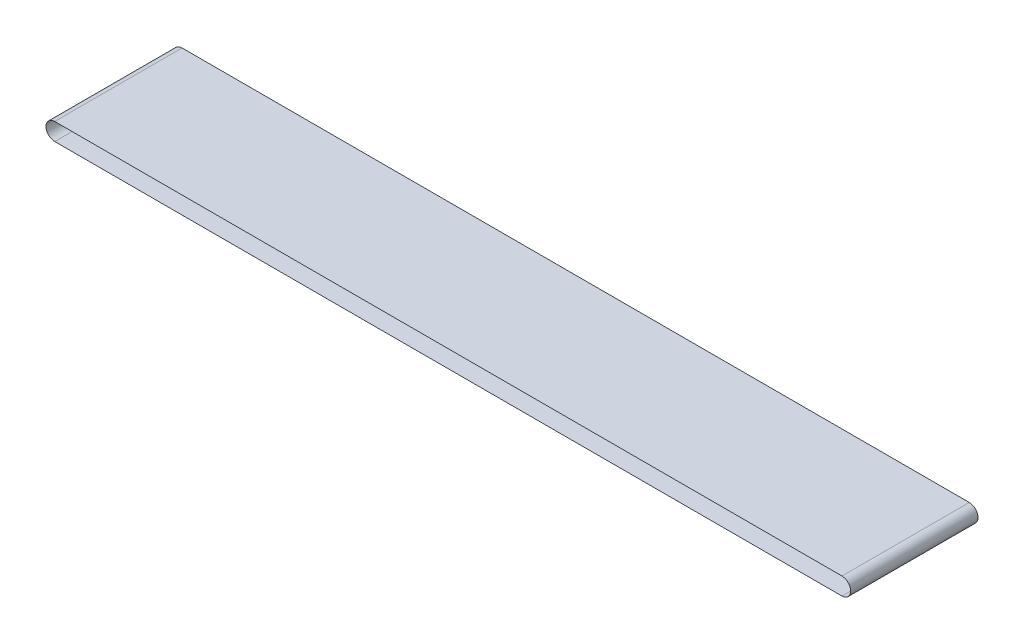
SolidWorks part; units mm, degrees
ref_plane "Front Plane" through (0, 0, 0) normal (0, 0, 1) x (1, 0, 0)
ref_plane "Top Plane" through (0, 0, 0) normal (0, 1, 0) x (1, 0, 0)
ref_plane "Right Plane" through (0, 0, 0) normal (1, 0, 0) x (0, 0, -1)
sketch "Sketch1" plane through (0, 0, 0) normal (0, 0, 1) x (1, 0, 0)
  line L0 (-3124.7397, 50) -> (275.2603, 50)
  line L1 (-3124.7397, -25) -> (275.2603, -25)
  arc A0 (-3124.7397, 50) -> (-3124.7397, -25) centre (-3124.7397, 12.5) ccw
  arc A1 (275.2603, -25) -> (275.2603, 50) centre (275.2603, 12.5) ccw
  dimension "D1" = 75
  dimension "D2" = 75
  dimension "D3" = 3400
extrude "Boss-Extrude1" add sketch "Sketch1" along normal blind 550
shell "Shell1" thickness 0.002
